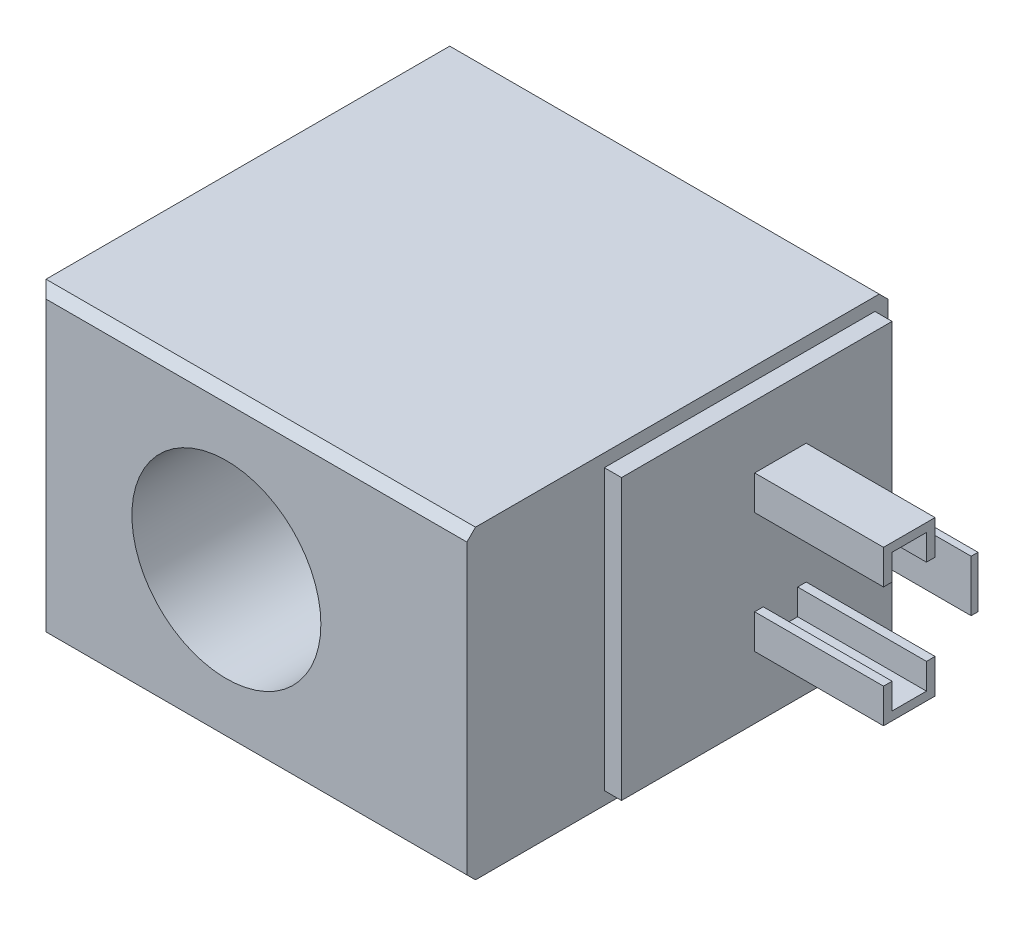
SolidWorks part; units mm, degrees
ref_plane "Front Plane" through (0, 0, 0) normal (0, 0, 1) x (1, 0, 0)
ref_plane "Top Plane" through (0, 0, 0) normal (0, 1, 0) x (1, 0, 0)
ref_plane "Right Plane" through (0, 0, 0) normal (1, 0, 0) x (0, 0, -1)
sketch "Sketch1" plane through (0, 0, 0) normal (0, 0, 1) x (1, 0, 0)
  line L0 (-25, 0) -> (-3, 0) construction
  line L1 (25, -17.78) -> (-25, -17.78)
  line L2 (25, -17.78) -> (25, 17.78)
  line L3 (25, 17.78) -> (-25, 17.78)
  line L4 (-25, -17.78) -> (-25, 17.78)
  line L5 (25, -17.78) -> (-25, 17.78) construction
  line L6 (25, 17.78) -> (-25, -17.78) construction
  circle A0 centre (-3, 0) radius 11
  point P0 (0, 0)
  dimension "D3" = 22
  dimension "D1" = 50
  dimension "D2" = 35.56
  dimension "D4" = 22
extrude "Boss-Extrude1" add sketch "Sketch1" along normal blind 49
sketch "Sketch2" plane through (25, 0, 0) normal (1, 0, 0) x (0, 0, -1)
  line L6 (-33, 16.28) -> (-33, -16.28)
  line L7 (-49, -17.78) -> (-49, 17.78) construction
  line L9 (-1.5, -16.28) -> (-49, -16.28)
  line L10 (-49, 16.28) -> (-1.5, 16.28)
  line L11 (-1.5, 16.28) -> (-1.5, -16.28)
  line L12 (-1.5, -16.28) -> (-33, -16.28)
  line L13 (-33, 16.28) -> (-1.5, 16.28)
  line L14 (-1.5, 16.28) -> (-1.5, -16.28)
  dimension "D2" = 16
  dimension "D1" = 1.5
extrude "Boss-Extrude2" add sketch "Sketch2" along normal blind 2
sketch "Sketch3" plane through (27, 0, 0) normal (1, 0, 0) x (0, 0, -1)
  line L0 (-33, 0) -> (-1.5, 0) construction
  line L1 (-33, 16.28) -> (-33, -16.28) construction
  line L2 (-1.5, -16.28) -> (-1.5, 16.28) construction
  line L3 (-16.5, 5) -> (-16.5, 8)
  line L4 (-17.5, 5) -> (-16.5, 5)
  line L5 (-17.5, 5) -> (-17.5, 9)
  line L6 (-17.5, 9) -> (-11.5, 9)
  line L7 (-11.5, 5) -> (-11.5, 9)
  line L8 (-7.3, 3) -> (-6.5, 3)
  line L9 (-7.3, 3) -> (-7.3, -3)
  line L11 (-6.5, 3) -> (-6.5, -3)
  line L12 (-16.5, 8) -> (-12.5, 8)
  line L13 (-12.5, 5) -> (-12.5, 8)
  line L14 (-12.5, 5) -> (-11.5, 5)
  line L15 (-7.3, -3) -> (-6.5, -3)
  line L16 (-12.5, -5) -> (-11.5, -5)
  line L17 (-12.5, -5) -> (-12.5, -8)
  line L18 (-16.5, -8) -> (-12.5, -8)
  line L19 (-11.5, -5) -> (-11.5, -9)
  line L20 (-17.5, -9) -> (-11.5, -9)
  line L21 (-17.5, -5) -> (-17.5, -9)
  line L22 (-17.5, -5) -> (-16.5, -5)
  line L23 (-16.5, -5) -> (-16.5, -8)
  point P19 (-6.5, 0)
  point P20 (-7.3, 0)
  dimension "D2" = 6
  dimension "D3" = 0.8
  dimension "D4" = 5
  dimension "D5" = 10
  dimension "D6" = 5
  dimension "D7" = 9
  dimension "D8" = 6
  dimension "D1" = 1
extrude "Boss-Extrude3" add sketch "Sketch3" along normal blind 15
chamfer "Chamfer1" distance 1 angle 45 6 edges at (0, 17.78, 49) (-25, 0, 49) (0, -17.78, 49) (0, -17.78, 0) (-25, 0, 0) (0, 17.78, 0)
